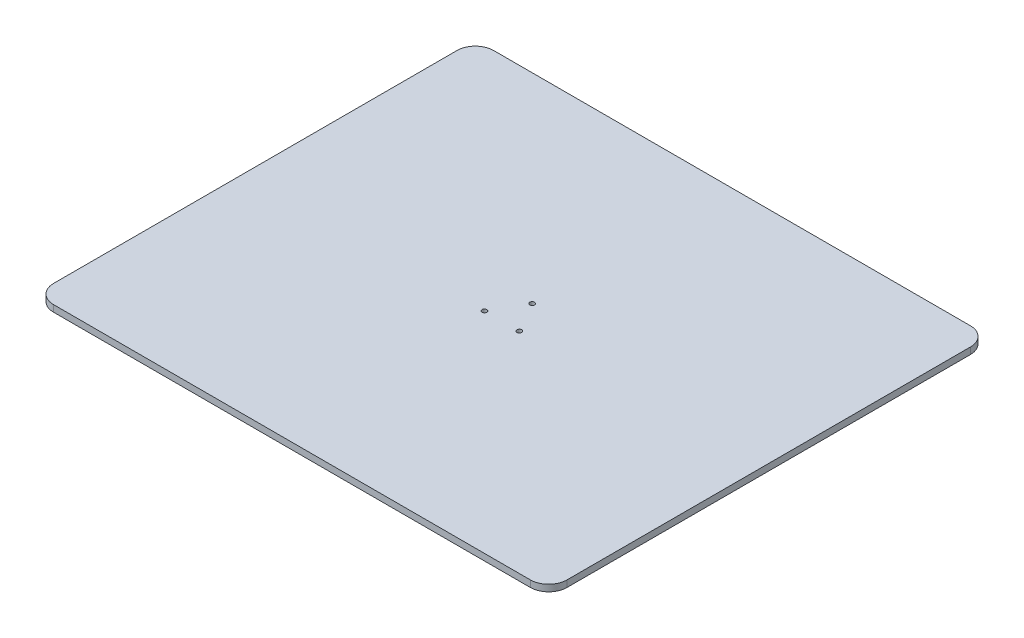
SolidWorks part; units mm, degrees
material "ABS"
ref_plane "Front Plane" through (0, 0, 0) normal (0, 0, 1) x (1, 0, 0)
ref_plane "Top Plane" through (0, 0, 0) normal (0, 1, 0) x (1, 0, 0)
ref_plane "Right Plane" through (0, 0, 0) normal (1, 0, 0) x (0, 0, -1)
sketch "Sketch1" plane through (0, 0, 0) normal (0, 1, 0) x (1, 0, 0)
  line L0 (55, 0) -> (-27.5, 47.6314) construction
  line L1 (-700, 600) -> (700, 600)
  line L2 (-700, 600) -> (-700, -600)
  line L3 (-700, -600) -> (700, -600)
  line L4 (700, 600) -> (700, -600)
  line L5 (0, -600) -> (0, 600) construction
  line L6 (-700, 0) -> (700, 0) construction
  line L7 (-27.5, 47.6314) -> (-27.5, -47.6314) construction
  line L8 (-27.5, -47.6314) -> (55, 0) construction
  line L9 (0, 0) -> (0, 55) construction
  line L10 (0, 55) -> (-47.6314, -27.5) construction
  line L11 (-47.6314, -27.5) -> (47.6314, -27.5) construction
  line L12 (47.6314, -27.5) -> (0, 55) construction
  circle A0 centre (0, 0) radius 75 construction
  circle A1 centre (0, 0) radius 55 construction
  circle A2 centre (0, 0) radius 27.5 construction
  circle A3 centre (0, 0) radius 27.5 construction
  circle A4 centre (0, 55) radius 6.5
  circle A5 centre (-47.6314, -27.5) radius 6.5
  circle A6 centre (47.6314, -27.5) radius 6.5
  point P0 (0, 0)
  dimension "D3" = 110
  dimension "D4" = 150
  dimension "D1" = 1400
  dimension "D2" = 1200
extrude "Boss-Extrude1" add sketch "Sketch1" along normal blind 18
sketch "Sketch2" plane through (0, 0, 0) normal (0, -1, 0) x (1, 0, 0)
  circle A0 centre (0, 0) radius 5
extrude "Cut-Extrude1" cut sketch "Sketch2" against normal blind 1
fillet "Fillet1" radius 50 4 edges at (700, 9, -600) (700, 9, 600) (-700, 9, 600) (-700, 9, -600)
sketch "Sketch3" plane through (0, 18, 0) normal (0, 1, 0) x (1, 0, 0)
  line L0 (-108.937, -219.6886) -> (-234.7326, -210.062)
  line L1 (-234.7326, -210.062) -> (-358.2136, -219.2576)
  line L2 (-24.6354, -235.7994) -> (-24.8453, -235.7994)
  line L3 (-40.5789, -291.8555) -> (-48.0791, -291.8555)
  line L4 (-63.7066, -235.7994) -> (-63.9144, -235.7994)
  line L5 (-68.808, -291.8555) -> (-79.9628, -291.8555)
  line L6 (-79.9628, -291.8555) -> (-71.9409, -220.1722)
  line L7 (-71.9409, -220.1722) -> (-58.6049, -220.1722)
  line L8 (-58.6049, -220.1722) -> (-45.7821, -266.1213)
  line L9 (-43.9096, -274.1443) -> (-43.7005, -274.1443)
  line L10 (-41.8247, -266.1213) -> (-28.5982, -220.1722)
  line L11 (-28.5982, -220.1722) -> (-15.2571, -220.1722)
  line L12 (-15.2571, -220.1722) -> (-7.2304, -291.8555)
  line L13 (-7.2304, -291.8555) -> (-19.7405, -291.8555)
  line L14 (4.7523, -235.6977) -> (17.4635, -235.6977)
  line L15 (17.4635, -235.6977) -> (17.4635, -291.8555)
  line L16 (17.4635, -291.8555) -> (4.7523, -291.8555)
  line L17 (4.7523, -291.8555) -> (4.7523, -235.6977)
  line L18 (62.3691, -283.5184) -> (62.3691, -243.0942)
  line L19 (62.3691, -236.2174) -> (62.3691, -210.0652)
  line L20 (62.3691, -210.0652) -> (75.0815, -210.0652)
  line L21 (75.0815, -210.0652) -> (75.0815, -288.8365)
  line L22 (119.5758, -283.5184) -> (119.5758, -243.0942)
  line L23 (119.5758, -236.2174) -> (119.5758, -210.0652)
  line L24 (119.5758, -210.0652) -> (132.2904, -210.0652)
  line L25 (132.2904, -210.0652) -> (132.2904, -288.8365)
  line L26 (146.9693, -210.0652) -> (159.6729, -210.0652)
  line L27 (159.6729, -210.0652) -> (159.6729, -291.8555)
  line L28 (159.6729, -291.8555) -> (146.9693, -291.8555)
  line L29 (146.9693, -291.8555) -> (146.9693, -210.0652)
  line L30 (183.0194, -261.9537) -> (206.2499, -258.4109)
  line L31 (213.2263, -280.9174) -> (216.2497, -288.9393)
  line L32 (218.1244, -263.4141) -> (183.7434, -268.415)
  line L33 (225.9145, -288.7294) -> (229.2617, -280.6033)
  line L34 (259.7856, -238.6117) -> (256.664, -246.0124)
  line L35 (281.883, -261.9537) -> (305.1112, -258.4109)
  line L36 (312.0987, -280.9174) -> (315.122, -288.9393)
  line L37 (316.988, -263.4141) -> (282.618, -268.415)
  line L38 (356.0547, -291.8555) -> (345.5278, -271.4349)
  line L39 (345.5278, -271.4349) -> (345.3244, -271.4349)
  line L40 (345.3244, -271.4349) -> (334.5832, -291.8555)
  line L41 (334.5832, -291.8555) -> (321.6674, -291.8555)
  line L42 (321.6674, -291.8555) -> (339.0722, -262.7895)
  line L43 (339.0722, -262.7895) -> (323.4394, -235.6977)
  line L44 (323.4394, -235.6977) -> (336.7839, -235.6977)
  line L45 (336.7839, -235.6977) -> (346.2608, -254.0335)
  line L46 (346.2608, -254.0335) -> (346.4664, -254.0335)
  line L47 (346.4664, -254.0335) -> (356.3632, -235.6977)
  line L48 (356.3632, -235.6977) -> (368.3383, -235.6977)
  line L49 (368.3383, -235.6977) -> (352.408, -261.9548)
  line L50 (352.408, -261.9548) -> (370.0119, -291.8555)
  line L51 (370.0119, -291.8555) -> (356.0547, -291.8555)
  line L52 (-77.3618, -371.7369) -> (-77.3618, -320.8951)
  line L53 (-77.3618, -320.8951) -> (-64.1232, -320.8951)
  line L54 (-64.1232, -320.8951) -> (-64.1232, -371.6363)
  line L55 (-42.3444, -371.6363) -> (-42.3444, -320.8951)
  line L56 (-42.3444, -320.8951) -> (-30.0518, -320.8951)
  line L57 (-30.0518, -320.8951) -> (-30.0518, -371.7369)
  line L58 (15.6893, -392.5764) -> (15.6893, -352.779)
  line L59 (-3.1681, -344.9679) -> (-3.1681, -392.5764)
  line L60 (-3.1681, -392.5764) -> (-15.8805, -392.5764)
  line L61 (-15.8805, -392.5764) -> (-15.8805, -339.4419)
  line L62 (28.4039, -352.5689) -> (28.4039, -392.5764)
  line L63 (28.4039, -392.5764) -> (15.6893, -392.5764)
  line L64 (42.3654, -336.4166) -> (55.0734, -336.4166)
  line L65 (55.0734, -336.4166) -> (55.0734, -392.572)
  line L66 (55.0734, -392.572) -> (42.3654, -392.572)
  line L67 (42.3654, -392.572) -> (42.3654, -336.4166)
  line L68 (94.8796, -392.5764) -> (82.7907, -392.5764)
  line L69 (82.7907, -392.5764) -> (64.454, -336.4197)
  line L70 (64.454, -336.4197) -> (77.9997, -336.4197)
  line L71 (77.9997, -336.4197) -> (87.8921, -372.6798)
  line L72 (89.253, -380.387) -> (89.4587, -380.387)
  line L73 (90.9199, -372.6798) -> (101.0203, -336.4197)
  line L74 (101.0203, -336.4197) -> (112.9013, -336.4197)
  line L75 (112.9013, -336.4197) -> (94.8796, -392.5764)
  line L76 (129.6629, -362.678) -> (152.8956, -359.1361)
  line L77 (159.8743, -381.6448) -> (162.9019, -389.6625)
  line L78 (164.7701, -364.1372) -> (130.3914, -369.1336)
  line L79 (189.0508, -345.1704) -> (189.0508, -392.5764)
  line L80 (189.0508, -392.5764) -> (176.3362, -392.5764)
  line L81 (176.3362, -392.5764) -> (176.3362, -339.441)
  line L82 (203.4345, -335.4791) -> (200.9273, -344.7569)
  line L83 (208.3216, -389.4568) -> (211.6511, -381.3276)
  line L84 (242.1817, -339.3391) -> (239.0643, -346.7378)
  line L85 (255.4214, -336.4166) -> (268.1337, -336.4166)
  line L86 (268.1337, -336.4166) -> (268.1337, -392.572)
  line L87 (268.1337, -392.572) -> (255.4214, -392.572)
  line L88 (255.4214, -392.572) -> (255.4214, -336.4166)
  line L89 (285.3221, -377.9893) -> (285.3221, -344.5467)
  line L90 (285.3221, -344.5467) -> (279.0784, -344.5467)
  line L91 (279.0784, -344.5467) -> (279.0784, -336.4166)
  line L92 (279.0784, -336.4166) -> (285.3221, -336.4166)
  line L93 (285.3221, -336.4166) -> (285.3221, -324.0181)
  line L94 (285.3221, -324.0181) -> (298.0432, -320.4785)
  line L95 (298.0432, -320.4785) -> (298.0432, -336.4166)
  line L96 (298.0432, -336.4166) -> (307.2026, -336.4166)
  line L97 (307.2026, -336.4166) -> (307.2026, -344.5467)
  line L98 (307.2026, -344.5467) -> (298.0432, -344.5467)
  line L99 (298.0432, -344.5467) -> (298.0432, -377.3679)
  line L100 (307.2026, -384.143) -> (307.2026, -392.0536)
  line L101 (336.0729, -414.9778) -> (322.63, -414.9778)
  line L102 (322.63, -414.9778) -> (331.796, -392.572)
  line L103 (331.796, -392.572) -> (313.2472, -336.4186)
  line L104 (313.2472, -336.4186) -> (326.8018, -336.4186)
  line L105 (326.8018, -336.4186) -> (336.4864, -372.7826)
  line L106 (337.6304, -380.809) -> (337.8406, -380.809)
  line L107 (339.3916, -372.7826) -> (349.8222, -336.4186)
  line L108 (349.8222, -336.4186) -> (361.7012, -336.4186)
  line L109 (361.7012, -336.4186) -> (336.0729, -414.9778)
  line L110 (-76.4178, -496.7756) -> (-76.4178, -425.0979)
  line L111 (-76.4178, -425.0979) -> (-66.8338, -425.0979)
  line L112 (-66.8338, -425.0979) -> (-66.8338, -490.3155)
  line L113 (-66.8338, -490.3155) -> (-45.2626, -490.3155)
  line L114 (-45.2626, -490.3155) -> (-45.2626, -496.7756)
  line L115 (-45.2626, -496.7756) -> (-76.4178, -496.7756)
  line L116 (50.2847, -496.7756) -> (50.2847, -456.4531)
  line L117 (27.8811, -447.497) -> (27.8811, -496.7756)
  line L118 (27.8811, -496.7756) -> (18.7149, -496.7756)
  line L119 (18.7149, -496.7756) -> (18.7149, -443.5286)
  line L120 (59.4574, -456.2497) -> (59.4574, -496.7756)
  line L121 (59.4574, -496.7756) -> (50.2847, -496.7756)
  line L122 (105.2927, -490.2149) -> (105.2927, -446.4491)
  line L123 (105.2927, -441.3431) -> (105.2927, -414.9821)
  line L124 (105.2927, -414.9821) -> (114.3605, -414.9821)
  line L125 (114.3605, -414.9821) -> (114.3605, -493.8661)
  line L126 (215.0113, -496.7756) -> (215.0113, -456.4531)
  line L127 (192.6099, -447.497) -> (192.6099, -496.7756)
  line L128 (192.6099, -496.7756) -> (183.4482, -496.7756)
  line L129 (183.4482, -496.7756) -> (183.4482, -443.5286)
  line L130 (224.1862, -456.2497) -> (224.1862, -496.7756)
  line L131 (224.1862, -496.7756) -> (215.0113, -496.7756)
  line L132 (-287.6033, -317.3665) -> (-287.8495, -317.476)
  line L133 (-283.8428, -360.4576) -> (-283.5695, -360.357)
  line L134 (-192.9487, -354.5454) -> (-186.1037, -360.9652)
  line L135 (-186.1037, -360.9652) -> (-145.5361, -360.9652)
  line L136 (-145.5361, -360.9652) -> (-145.5361, -360.2519)
  line L137 (-277.5347, -373.0626) -> (-277.7809, -373.1612)
  line L138 (-275.9499, -402.3069) -> (-275.9958, -402.3069)
  line L139 (-274.3748, -408.5417) -> (-274.1517, -408.4521)
  line L140 (-201.5593, -403.3986) -> (-195.3584, -408.8304)
  line L141 (-195.3584, -408.8304) -> (-162.7178, -408.8304)
  line L142 (-162.7178, -408.8304) -> (-162.7178, -408.1152)
  line L143 (-231.3232, -424.039) -> (-231.8711, -424.0345)
  line L144 (-264.1125, -430.4095) -> (-265.003, -430.72)
  line L145 (-266.9904, -420.6875) -> (-267.1687, -420.7664)
  line L146 (-264.2767, -450.8113) -> (-264.037, -450.715)
  line L147 (-210.0286, -445.6659) -> (-205.3461, -449.4549)
  line L148 (-205.3461, -449.4549) -> (-180.6346, -449.4549)
  line L149 (-180.6346, -449.4549) -> (-180.6346, -448.7417)
  line L150 (-204.3125, -247.2035) -> (-207.3172, -248.2963)
  line L151 (-207.3172, -248.2963) -> (-205.3165, -253.8025)
  line L152 (-230.9809, -246.1775) -> (-226.8288, -242.0398)
  line L153 (-226.8288, -242.0398) -> (-229.0962, -239.7799)
  line L154 (-239.3222, -239.7777) -> (-241.5767, -242.0342)
  line L155 (-241.5767, -242.0342) -> (-237.4244, -246.1896)
  line L156 (-262.6327, -253.7983) -> (-260.6331, -248.2963)
  line L157 (-260.6331, -248.2963) -> (-263.6412, -247.2035)
  line L158 (-272.9102, -251.5263) -> (-273.9951, -254.5279)
  line L159 (-273.9951, -254.5279) -> (-268.4474, -256.5492)
  line L160 (-199.528, -256.5579) -> (-193.9518, -254.5279)
  line L161 (-193.9518, -254.5279) -> (-195.0412, -251.5263)
  spline S0 degree 2 poles (-358.2136, -219.2576) (-359.0843, -246.2586) (-359.0843, -279.7218) knots 2 2 2 3 3 3
  spline S1 degree 2 poles (-359.0843, -279.7218) (-359.0843, -451.1395) (-233.9723, -496.7953) knots 3 3 3 4 4 4
  spline S2 degree 2 poles (-233.9723, -496.7953) (-108.0609, -451.5748) (-108.0609, -280.1549) knots 4 4 4 5 5 5
  spline S3 degree 2 poles (-108.0609, -280.1549) (-108.0609, -246.6939) (-108.937, -219.6886) knots 5 5 5 6 6 6
  spline S4 degree 2 poles (-19.7405, -291.8555) (-19.8402, -290.0867) (-24.3225, -244.4495) knots 0 0 0 1 1 1
  spline S5 degree 2 poles (-24.3225, -244.4495) (-24.7337, -239.9659) (-24.6354, -235.7994) knots 1 1 1 2 2 2
  spline S6 degree 2 poles (-24.8453, -235.7994) (-25.5716, -239.863) (-26.9226, -244.4495) knots 3 3 3 4 4 4
  spline S7 degree 2 poles (-26.9226, -244.4495) (-39.742, -289.4622) (-40.5789, -291.8555) knots 4 4 4 5 5 5
  spline S8 degree 2 poles (-48.0791, -291.8555) (-48.8043, -289.7729) (-61.6185, -244.3433) knots 6 6 6 7 7 7
  spline S9 degree 2 poles (-61.6185, -244.3433) (-62.8676, -239.863) (-63.7066, -235.7994) knots 7 7 7 8 8 8
  spline S10 degree 2 poles (-63.9144, -235.7994) (-63.8136, -239.863) (-64.226, -244.3433) knots 9 9 9 10 10 10
  spline S11 degree 2 poles (-64.226, -244.3433) (-68.7086, -289.7729) (-68.808, -291.8555) knots 10 10 10 11 11 11
  spline S12 degree 2 poles (-45.7821, -266.1213) (-44.5395, -270.7021) (-43.9096, -274.1443) knots 15 15 15 16 16 16
  spline S13 degree 2 poles (-43.7005, -274.1443) (-43.1788, -270.7021) (-41.8247, -266.1213) knots 17 17 17 18 18 18
  spline S14 degree 3 poles (11.1107, -213.4003) (15.0724, -213.4003) (18.0892, -216.2103) (18.0892, -219.7553) (18.0892, -223.1922) (15.0724, -226.0064) (11.1107, -226.0064) knots 2 2 2 2 3 3 3 4 4 4 4
  spline S15 degree 3 poles (11.1107, -226.0064) (7.2539, -226.0064) (4.1298, -223.1922) (4.1298, -219.7553) (4.1298, -216.2103) (7.2539, -213.4003) (11.1107, -213.4003) knots 0 0 0 0 1 1 1 2 2 2 2
  spline S16 degree 3 poles (62.3691, -243.0942) (60.5992, -242.5725) (58.7267, -242.3657) (56.7446, -242.3657) knots 0 0 0 0 1 1 1 1
  spline S17 degree 3 poles (56.7446, -242.3657) (45.6949, -242.3657) (41.9453, -251.8458) (41.9453, -263.7268) knots 1 1 1 1 2 2 2 2
  spline S18 degree 3 poles (41.9453, -263.7268) (41.9453, -276.4371) (46.0166, -284.772) (55.8127, -284.772) knots 2 2 2 2 3 3 3 3
  spline S19 degree 3 poles (55.8127, -284.772) (58.823, -284.772) (60.9144, -284.4602) (62.3691, -283.5184) knots 3 3 3 3 4 4 4 4
  spline S20 degree 3 poles (55.4935, -292.899) (38.9243, -292.899) (29.3423, -282.2713) (29.3423, -264.4542) knots 0 0 0 0 1 1 1 1
  spline S21 degree 3 poles (29.3423, -264.4542) (29.3423, -246.1175) (39.3443, -235.1749) (53.9357, -235.1749) knots 1 1 1 1 2 2 2 2
  spline S22 degree 3 poles (53.9357, -235.1749) (57.064, -235.1749) (59.8729, -235.4898) (62.3691, -236.2174) knots 2 2 2 2 3 3 3 3
  spline S23 degree 3 poles (75.0815, -288.8365) (70.6012, -291.3381) (64.2439, -292.899) (55.4935, -292.899) knots 6 6 6 6 7 7 7 7
  spline S24 degree 3 poles (119.5758, -243.0942) (117.8081, -242.5725) (115.9158, -242.3657) (113.947, -242.3657) knots 0 0 0 0 1 1 1 1
  spline S25 degree 3 poles (113.947, -242.3657) (102.9038, -242.3657) (99.1542, -251.8458) (99.1542, -263.7268) knots 1 1 1 1 2 2 2 2
  spline S26 degree 3 poles (99.1542, -263.7268) (99.1542, -276.4371) (103.208, -284.772) (113.0063, -284.772) knots 2 2 2 2 3 3 3 3
  spline S27 degree 3 poles (113.0063, -284.772) (116.0339, -284.772) (118.1078, -284.4602) (119.5758, -283.5184) knots 3 3 3 3 4 4 4 4
  spline S28 degree 3 poles (112.7044, -292.899) (96.1309, -292.899) (86.5447, -282.2713) (86.5447, -264.4542) knots 0 0 0 0 1 1 1 1
  spline S29 degree 3 poles (86.5447, -264.4542) (86.5447, -246.1175) (96.5465, -235.1749) (111.1316, -235.1749) knots 1 1 1 1 2 2 2 2
  spline S30 degree 3 poles (111.1316, -235.1749) (114.2577, -235.1749) (117.0753, -235.4898) (119.5758, -236.2174) knots 2 2 2 2 3 3 3 3
  spline S31 degree 3 poles (132.2904, -288.8365) (127.8078, -291.3381) (121.4528, -292.899) (112.7044, -292.899) knots 6 6 6 6 7 7 7 7
  spline S32 degree 3 poles (195.2002, -242.4663) (187.8104, -242.4663) (182.7045, -248.5129) (183.0194, -261.9537) knots 0 0 0 0 1 1 1 1
  spline S33 degree 3 poles (206.2499, -258.4109) (206.2499, -247.0548) (202.1831, -242.4663) (195.2002, -242.4663) knots 2 2 2 2 3 3 3 3
  spline S34 degree 3 poles (183.7434, -268.415) (184.7782, -278.8336) (189.7835, -284.039) (199.0548, -284.039) knots 0 0 0 0 1 1 1 1
  spline S35 degree 3 poles (199.0548, -284.039) (205.5172, -284.039) (210.2096, -282.4803) (213.2263, -280.9174) knots 1 1 1 1 2 2 2 2
  spline S36 degree 3 poles (216.2497, -288.9393) (212.29, -291.1271) (206.2499, -292.899) (197.7029, -292.899) knots 3 3 3 3 4 4 4 4
  spline S37 degree 3 poles (197.7029, -292.899) (181.7636, -292.899) (171.6525, -282.5843) (171.6525, -263.6208) knots 4 4 4 4 5 5 5 5
  spline S38 degree 3 poles (171.6525, -263.6208) (171.6525, -245.2828) (180.9303, -234.6531) (195.6312, -234.6531) knots 5 5 5 5 6 6 6 6
  spline S39 degree 3 poles (195.6312, -234.6531) (210.518, -234.6531) (218.6428, -244.5532) (218.1244, -263.4141) knots 6 6 6 6 7 7 7 7
  spline S40 degree 3 poles (241.4467, -292.7951) (234.8818, -292.7951) (229.2617, -291.0242) (225.9145, -288.7294) knots 0 0 0 0 1 1 1 1
  spline S41 degree 3 poles (229.2617, -280.6033) (231.3444, -282.2713) (235.1968, -283.8356) (239.7821, -283.8356) knots 2 2 2 2 3 3 3 3
  spline S42 degree 3 poles (239.7821, -283.8356) (244.9864, -283.8356) (248.4209, -280.4983) (248.4209, -275.9131) knots 3 3 3 3 4 4 4 4
  spline S43 degree 3 poles (248.4209, -275.9131) (248.4209, -271.121) (245.9227, -268.8296) (240.1911, -266.6441) knots 4 4 4 4 5 5 5 5
  spline S44 degree 3 poles (240.1911, -266.6441) (229.5679, -262.5794) (227.3825, -256.7472) (227.3825, -250.9105) knots 5 5 5 5 6 6 6 6
  spline S45 degree 3 poles (227.3825, -250.9105) (227.3825, -241.9479) (234.4595, -234.6531) (245.1963, -234.6531) knots 6 6 6 6 7 7 7 7
  spline S46 degree 3 poles (245.1963, -234.6531) (251.4442, -234.6531) (256.1259, -236.2174) (259.7856, -238.6117) knots 7 7 7 7 8 8 8 8
  spline S47 degree 3 poles (256.664, -246.0124) (254.9969, -244.6551) (251.6586, -242.8863) (247.699, -242.8863) knots 9 9 9 9 10 10 10 10
  spline S48 degree 3 poles (247.699, -242.8863) (242.4837, -242.8863) (239.6748, -246.3263) (239.6748, -250.2817) knots 10 10 10 10 11 11 11 11
  spline S49 degree 3 poles (239.6748, -250.2817) (239.6748, -254.8668) (243.1138, -257.1574) (248.0074, -259.1394) knots 11 11 11 11 12 12 12 12
  spline S50 degree 3 poles (248.0074, -259.1394) (258.9523, -263.5169) (261.4505, -269.1446) (261.4505, -275.7041) knots 12 12 12 12 13 13 13 13
  spline S51 degree 3 poles (261.4505, -275.7041) (261.4505, -284.8757) (253.7368, -292.7951) (241.4467, -292.7951) knots 13 13 13 13 14 14 14 14
  spline S52 degree 3 poles (294.0725, -242.4663) (286.6673, -242.4663) (281.5658, -248.5129) (281.883, -261.9537) knots 0 0 0 0 1 1 1 1
  spline S53 degree 3 poles (305.1112, -258.4109) (305.1112, -247.0548) (301.0532, -242.4663) (294.0725, -242.4663) knots 2 2 2 2 3 3 3 3
  spline S54 degree 3 poles (282.618, -268.415) (283.6572, -278.8336) (288.6559, -284.039) (297.9206, -284.039) knots 0 0 0 0 1 1 1 1
  spline S55 degree 3 poles (297.9206, -284.039) (304.3828, -284.039) (309.0709, -282.4803) (312.0987, -280.9174) knots 1 1 1 1 2 2 2 2
  spline S56 degree 3 poles (315.122, -288.9393) (311.1623, -291.1271) (305.1112, -292.899) (296.5707, -292.899) knots 3 3 3 3 4 4 4 4
  spline S57 degree 3 poles (296.5707, -292.899) (280.6317, -292.899) (270.5271, -282.5843) (270.5271, -263.6208) knots 4 4 4 4 5 5 5 5
  spline S58 degree 3 poles (270.5271, -263.6208) (270.5271, -245.2828) (279.7916, -234.6531) (294.4816, -234.6531) knots 5 5 5 5 6 6 6 6
  spline S59 degree 3 poles (294.4816, -234.6531) (309.3881, -234.6531) (317.5151, -244.5532) (316.988, -263.4141) knots 6 6 6 6 7 7 7 7
  spline S60 degree 3 poles (-53.7057, -393.725) (-67.769, -393.725) (-77.3618, -384.7599) (-77.3618, -371.7369) knots 0 0 0 0 1 1 1 1
  spline S61 degree 3 poles (-64.1232, -371.6363) (-64.1232, -379.3455) (-59.1158, -383.5108) (-53.1797, -383.5108) knots 4 4 4 4 5 5 5 5
  spline S62 degree 3 poles (-53.1797, -383.5108) (-47.1407, -383.5108) (-42.3444, -379.3455) (-42.3444, -371.6363) knots 5 5 5 5 6 6 6 6
  spline S63 degree 3 poles (-30.0518, -371.7369) (-30.0518, -384.7599) (-39.6372, -393.725) (-53.7057, -393.725) knots 9 9 9 9 10 10 10 10
  spline S64 degree 3 poles (15.6893, -352.779) (15.6893, -348.1948) (13.6024, -343.4027) (5.5868, -343.4027) knots 1 1 1 1 2 2 2 2
  spline S65 degree 3 poles (5.5868, -343.4027) (1.4161, -343.4027) (-0.7705, -344.023) (-3.1681, -344.9679) knots 2 2 2 2 3 3 3 3
  spline S66 degree 3 poles (-15.8805, -339.4419) (-10.5689, -336.9437) (-3.3792, -335.3839) (6.1065, -335.3839) knots 6 6 6 6 7 7 7 7
  spline S67 degree 3 poles (6.1065, -335.3839) (22.8802, -335.3839) (28.4039, -343.5044) (28.4039, -352.5689) knots 7 7 7 7 8 8 8 8
  spline S68 degree 3 poles (48.7227, -314.1212) (52.6888, -314.1212) (55.6989, -316.9377) (55.6989, -320.4785) (55.6989, -323.9187) (52.6888, -326.7307) (48.7227, -326.7307) knots 2 2 2 2 3 3 3 4 4 4 4
  spline S69 degree 3 poles (48.7227, -326.7307) (44.8723, -326.7307) (41.7374, -323.9187) (41.7374, -320.4785) (41.7374, -316.9377) (44.8723, -314.1212) (48.7227, -314.1212) knots 0 0 0 0 1 1 1 2 2 2 2
  spline S70 degree 2 poles (87.8921, -372.6798) (89.0451, -376.7445) (89.253, -380.387) knots 4 4 4 5 5 5
  spline S71 degree 2 poles (89.4587, -380.387) (89.7779, -376.8473) (90.9199, -372.6798) knots 6 6 6 7 7 7
  spline S72 degree 3 poles (141.8524, -343.1928) (134.4494, -343.1928) (129.3392, -349.236) (129.6629, -362.678) knots 0 0 0 0 1 1 1 1
  spline S73 degree 3 poles (152.8956, -359.1361) (152.8956, -347.7802) (148.8354, -343.1928) (141.8524, -343.1928) knots 2 2 2 2 3 3 3 3
  spline S74 degree 3 poles (130.3914, -369.1336) (131.4306, -379.5579) (136.4292, -384.7599) (145.6983, -384.7599) knots 0 0 0 0 1 1 1 1
  spline S75 degree 3 poles (145.6983, -384.7599) (152.1606, -384.7599) (156.8508, -383.2046) (159.8743, -381.6448) knots 1 1 1 1 2 2 2 2
  spline S76 degree 3 poles (162.9019, -389.6625) (158.9335, -391.8502) (152.8956, -393.6199) (144.3421, -393.6199) knots 3 3 3 3 4 4 4 4
  spline S77 degree 3 poles (144.3421, -393.6199) (128.4073, -393.6199) (118.3005, -383.3052) (118.3005, -364.3429) knots 4 4 4 4 5 5 5 5
  spline S78 degree 3 poles (118.3005, -364.3429) (118.3005, -346.0028) (127.5672, -335.3817) (142.2594, -335.3817) knots 5 5 5 5 6 6 6 6
  spline S79 degree 3 poles (142.2594, -335.3817) (157.1615, -335.3817) (165.2952, -345.2786) (164.7701, -364.1372) knots 6 6 6 6 7 7 7 7
  spline S80 degree 3 poles (200.9273, -344.7569) (196.6572, -343.301) (191.9712, -343.5044) (189.0508, -345.1704) knots 0 0 0 0 1 1 1 1
  spline S81 degree 3 poles (176.3362, -339.441) (182.1662, -336.6276) (189.2564, -335.0624) (203.4345, -335.4791) knots 4 4 4 4 5 5 5 5
  spline S82 degree 3 poles (223.8451, -393.5171) (217.2844, -393.5171) (211.6511, -391.7364) (208.3216, -389.4568) knots 0 0 0 0 1 1 1 1
  spline S83 degree 3 poles (211.6511, -381.3276) (213.7382, -382.999) (217.6016, -384.5565) (222.1824, -384.5565) knots 2 2 2 2 3 3 3 3
  spline S84 degree 3 poles (222.1824, -384.5565) (227.389, -384.5565) (230.8323, -381.2248) (230.8323, -376.6372) knots 3 3 3 3 4 4 4 4
  spline S85 degree 3 poles (230.8323, -376.6372) (230.8323, -371.8464) (228.3276, -369.5536) (222.6002, -367.3617) knots 4 4 4 4 5 5 5 5
  spline S86 degree 3 poles (222.6002, -367.3617) (211.9705, -363.3014) (209.783, -357.4726) (209.783, -351.6337) knots 5 5 5 5 6 6 6 6
  spline S87 degree 3 poles (209.783, -351.6337) (209.783, -342.6666) (216.8708, -335.3839) (227.6013, -335.3839) knots 6 6 6 6 7 7 7 7
  spline S88 degree 3 poles (227.6013, -335.3839) (233.8535, -335.3839) (238.5372, -336.9415) (242.1817, -339.3391) knots 7 7 7 7 8 8 8 8
  spline S89 degree 3 poles (239.0643, -346.7378) (237.4062, -345.3792) (234.0634, -343.6117) (230.0995, -343.6117) knots 9 9 9 9 10 10 10 10
  spline S90 degree 3 poles (230.0995, -343.6117) (224.8885, -343.6117) (222.0861, -347.0483) (222.0861, -351.0057) knots 10 10 10 10 11 11 11 11
  spline S91 degree 3 poles (222.0861, -351.0057) (222.0861, -355.5922) (225.5164, -357.8827) (230.4167, -359.8581) knots 11 11 11 11 12 12 12 12
  spline S92 degree 3 poles (230.4167, -359.8581) (241.3527, -364.242) (243.8531, -369.8731) (243.8531, -376.4315) knots 12 12 12 12 13 13 13 13
  spline S93 degree 3 poles (243.8531, -376.4315) (243.8531, -385.5977) (236.1418, -393.5171) (223.8451, -393.5171) knots 13 13 13 13 14 14 14 14
  spline S94 degree 3 poles (261.7829, -314.1212) (265.7361, -314.1212) (268.7616, -316.9377) (268.7616, -320.4785) (268.7616, -323.9187) (265.7361, -326.7307) (261.7829, -326.7307) knots 2 2 2 2 3 3 3 4 4 4 4
  spline S95 degree 3 poles (261.7829, -326.7307) (257.9241, -326.7307) (254.7957, -323.9187) (254.7957, -320.4785) (254.7957, -316.9377) (257.9241, -314.1212) (261.7829, -314.1212) knots 0 0 0 0 1 1 1 2 2 2 2
  spline S96 degree 3 poles (300.7492, -393.2021) (289.6973, -393.2021) (285.3221, -385.8079) (285.3221, -377.9893) knots 0 0 0 0 1 1 1 1
  spline S97 degree 3 poles (298.0432, -377.3679) (298.0432, -381.7476) (299.8086, -384.6593) (304.1838, -384.6593) knots 12 12 12 12 13 13 13 13
  spline S98 degree 3 poles (304.1838, -384.6593) (305.3301, -384.6593) (306.1679, -384.4515) (307.2026, -384.143) knots 13 13 13 13 14 14 14 14
  spline S99 degree 3 poles (307.2026, -392.0536) (306.0564, -392.5764) (303.7638, -393.2021) (300.7492, -393.2021) knots 15 15 15 15 16 16 16 16
  spline S100 degree 2 poles (336.4864, -372.7826) (337.6304, -377.1623) (337.6304, -380.809) knots 5 5 5 6 6 6
  spline S101 degree 2 poles (337.8406, -380.809) (338.1578, -377.1623) (339.3916, -372.7826) knots 7 7 7 8 8 8
  spline S102 degree 3 poles (-15.7765, -491.4663) (-5.0429, -491.4663) (-3.0676, -480.003) (-3.0676, -468.7477) (-3.0676, -457.4966) (-5.0429, -445.4079) (-15.7765, -445.4079) knots 2 2 2 2 3 3 3 4 4 4 4
  spline S103 degree 3 poles (-15.7765, -445.4079) (-26.5079, -445.4079) (-28.596, -457.3917) (-28.596, -468.7477) (-28.596, -480.1126) (-26.3056, -491.4663) (-15.7765, -491.4663) knots 0 0 0 0 1 1 1 2 2 2 2
  spline S104 degree 3 poles (-15.8805, -439.5777) (-0.4632, -439.5777) (6.1065, -451.9751) (6.1065, -468.7477) (6.1065, -485.214) (-0.566, -497.8258) (-15.7765, -497.8258) knots 2 2 2 2 3 3 3 4 4 4 4
  spline S105 degree 3 poles (-15.7765, -497.8258) (-31.0986, -497.8258) (-37.7633, -485.214) (-37.7633, -468.7477) (-37.7633, -451.9751) (-30.9871, -439.5777) (-15.8805, -439.5777) knots 0 0 0 0 1 1 1 2 2 2 2
  spline S106 degree 3 poles (50.2847, -456.4531) (50.2847, -451.2443) (48.0992, -445.515) (38.5085, -445.515) knots 1 1 1 1 2 2 2 2
  spline S107 degree 3 poles (38.5085, -445.515) (33.3065, -445.515) (30.8015, -446.2457) (27.8811, -447.497) knots 2 2 2 2 3 3 3 3
  spline S108 degree 3 poles (18.7149, -443.5286) (23.718, -441.1375) (30.2787, -439.5777) (39.2435, -439.5777) knots 6 6 6 6 7 7 7 7
  spline S109 degree 3 poles (39.2435, -439.5777) (54.8589, -439.5777) (59.4574, -448.2255) (59.4574, -456.2497) knots 7 7 7 7 8 8 8 8
  spline S110 degree 3 poles (105.2927, -446.4491) (103.0044, -445.8279) (100.7118, -445.4079) (98.3097, -445.4079) knots 0 0 0 0 1 1 1 1
  spline S111 degree 3 poles (98.3097, -445.4079) (85.2934, -445.4079) (81.1258, -456.6565) (81.1258, -468.8505) knots 1 1 1 1 2 2 2 2
  spline S112 degree 3 poles (81.1258, -468.8505) (81.1258, -482.0857) (85.7069, -491.7747) (97.1679, -491.7747) knots 2 2 2 2 3 3 3 3
  spline S113 degree 3 poles (97.1679, -491.7747) (100.9217, -491.7747) (103.5207, -491.3612) (105.2927, -490.2149) knots 3 3 3 3 4 4 4 4
  spline S114 degree 3 poles (96.7479, -497.8258) (80.7125, -497.8258) (72.0582, -486.5682) (72.0582, -469.5812) knots 0 0 0 0 1 1 1 1
  spline S115 degree 3 poles (72.0582, -469.5812) (72.0582, -450.9339) (81.9551, -440.0918) (96.4349, -440.0918) knots 1 1 1 1 2 2 2 2
  spline S116 degree 3 poles (96.4349, -440.0918) (99.5588, -440.0918) (102.2738, -440.5163) (105.2927, -441.3431) knots 2 2 2 2 3 3 3 3
  spline S117 degree 3 poles (114.3605, -493.8661) (110.6087, -496.1544) (104.5664, -497.8258) (96.7479, -497.8258) knots 6 6 6 6 7 7 7 7
  spline S118 degree 3 poles (148.9536, -491.4663) (159.6949, -491.4663) (161.6702, -480.003) (161.6702, -468.7477) (161.6702, -457.4966) (159.6949, -445.4079) (148.9536, -445.4079) knots 2 2 2 2 3 3 3 4 4 4 4
  spline S119 degree 3 poles (148.9536, -445.4079) (138.2296, -445.4079) (136.134, -457.3917) (136.134, -468.7477) (136.134, -480.1126) (138.4333, -491.4663) (148.9536, -491.4663) knots 0 0 0 0 1 1 1 2 2 2 2
  spline S120 degree 3 poles (148.8486, -439.5777) (164.267, -439.5777) (170.8387, -451.9751) (170.8387, -468.7477) (170.8387, -485.214) (164.1707, -497.8258) (148.9536, -497.8258) knots 2 2 2 2 3 3 3 4 4 4 4
  spline S121 degree 3 poles (148.9536, -497.8258) (133.6378, -497.8258) (126.9765, -485.214) (126.9765, -468.7477) (126.9765, -451.9751) (133.7494, -439.5777) (148.8486, -439.5777) knots 0 0 0 0 1 1 1 2 2 2 2
  spline S122 degree 3 poles (215.0113, -456.4531) (215.0113, -451.2443) (212.8281, -445.515) (203.2463, -445.515) knots 1 1 1 1 2 2 2 2
  spline S123 degree 3 poles (203.2463, -445.515) (198.031, -445.515) (195.5284, -446.2457) (192.6099, -447.497) knots 2 2 2 2 3 3 3 3
  spline S124 degree 3 poles (183.4482, -443.5286) (188.4491, -441.1375) (195.0033, -439.5777) (203.9681, -439.5777) knots 6 6 6 6 7 7 7 7
  spline S125 degree 3 poles (203.9681, -439.5777) (219.5966, -439.5777) (224.1862, -448.2255) (224.1862, -456.2497) knots 7 7 7 7 8 8 8 8
  spline S126 degree 3 poles (-229.5523, -319.5531) (-254.0144, -319.5531) (-276.1806, -327.4932) (-285.2594, -331.2363) knots 0 0 0 0 1 1 1 1
  spline S127 degree 3 poles (-285.2594, -331.2363) (-286.2547, -328.0893) (-285.9397, -326.0067) (-285.3885, -324.7159) knots 1 1 1 1 2 2 2 2
  spline S128 degree 3 poles (-285.3885, -324.7159) (-283.3013, -324.5398) (-281.653, -322.8544) (-281.653, -320.81) knots 2 2 2 2 3 3 3 3
  spline S129 degree 3 poles (-281.653, -320.81) (-281.653, -318.6496) (-283.4906, -316.8951) (-285.7516, -316.8951) knots 3 3 3 3 4 4 4 4
  spline S130 degree 3 poles (-285.7516, -316.8951) (-285.9516, -316.8951) (-286.1113, -316.9388) (-286.3159, -316.9935) knots 4 4 4 4 5 5 5 5
  spline S131 degree 3 poles (-286.3159, -316.9935) (-286.5435, -317.0188) (-286.7502, -317.0602) (-286.981, -317.1248) knots 5 5 5 5 6 6 6 6
  spline S132 degree 3 poles (-286.981, -317.1248) (-287.2063, -317.1884) (-287.4086, -317.2726) (-287.6033, -317.3665) knots 6 6 6 6 7 7 7 7
  spline S133 degree 3 poles (-287.8495, -317.476) (-287.8988, -317.511) (-288.0889, -317.6335) (-288.2979, -317.8062) knots 8 8 8 8 9 9 9 9
  spline S134 degree 3 poles (-288.2979, -317.8062) (-288.463, -317.9343) (-288.6098, -318.0513) (-288.7321, -318.1693) knots 9 9 9 9 10 10 10 10
  spline S135 degree 3 poles (-288.7321, -318.1693) (-290.0645, -319.377) (-294.1346, -323.8967) (-291.7621, -332.4175) knots 10 10 10 10 11 11 11 11
  spline S136 degree 3 poles (-291.7621, -332.4175) (-293.1534, -332.9908) (-294.1673, -334.243) (-294.6552, -335.9397) knots 11 11 11 11 12 12 12 12
  spline S137 degree 3 poles (-294.6552, -335.9397) (-295.9984, -335.2636) (-297.4117, -335.1379) (-298.6335, -335.6126) knots 12 12 12 12 13 13 13 13
  spline S138 degree 3 poles (-298.6335, -335.6126) (-300.0795, -336.1682) (-301.1393, -337.495) (-301.5923, -339.2549) knots 13 13 13 13 14 14 14 14
  spline S139 degree 3 poles (-301.5923, -339.2549) (-302.9431, -338.5167) (-304.3683, -338.3689) (-305.6044, -338.8339) knots 14 14 14 14 15 15 15 15
  spline S140 degree 3 poles (-305.6044, -338.8339) (-307.0799, -339.4059) (-308.1169, -340.7645) (-308.5127, -342.5671) knots 15 15 15 15 16 16 16 16
  spline S141 degree 3 poles (-308.5127, -342.5671) (-309.8582, -341.7663) (-311.3391, -341.586) (-312.5752, -342.0694) knots 16 16 16 16 17 17 17 17
  spline S142 degree 3 poles (-312.5752, -342.0694) (-314.0508, -342.6415) (-315.0714, -344.0591) (-315.4137, -345.9164) knots 17 17 17 17 18 18 18 18
  spline S143 degree 3 poles (-315.4137, -345.9164) (-316.747, -345.0346) (-318.2358, -344.7974) (-319.5472, -345.2929) knots 18 18 18 18 19 19 19 19
  spline S144 degree 3 poles (-319.5472, -345.2929) (-322.1319, -346.3023) (-323.1502, -349.9656) (-321.8048, -353.456) knots 19 19 19 19 20 20 20 20
  spline S145 degree 3 poles (-321.8048, -353.456) (-320.465, -356.9146) (-317.26, -358.9874) (-314.625, -357.9681) knots 20 20 20 20 21 21 21 21
  spline S146 degree 3 poles (-314.625, -357.9681) (-313.2786, -357.4385) (-312.3225, -356.1643) (-311.9518, -354.5006) knots 21 21 21 21 22 22 22 22
  spline S147 degree 3 poles (-311.9518, -354.5006) (-310.5123, -355.5212) (-308.8584, -355.8252) (-307.4518, -355.2815) knots 22 22 22 22 23 23 23 23
  spline S148 degree 3 poles (-307.4518, -355.2815) (-306.1185, -354.7598) (-305.1438, -353.5534) (-304.7161, -351.9486) knots 23 23 23 23 24 24 24 24
  spline S149 degree 3 poles (-304.7161, -351.9486) (-303.2778, -352.8839) (-301.6599, -353.1278) (-300.2852, -352.5951) knots 24 24 24 24 25 25 25 25
  spline S150 degree 3 poles (-300.2852, -352.5951) (-298.9561, -352.0844) (-297.9794, -350.9184) (-297.5067, -349.3346) knots 25 25 25 25 26 26 26 26
  spline S151 degree 3 poles (-297.5067, -349.3346) (-296.0443, -350.2237) (-294.4473, -350.4271) (-293.1064, -349.9087) knots 26 26 26 26 27 27 27 27
  spline S152 degree 3 poles (-293.1064, -349.9087) (-291.8004, -349.4034) (-290.8136, -348.2723) (-290.2986, -346.7367) knots 27 27 27 27 28 28 28 28
  spline S153 degree 3 poles (-290.2986, -346.7367) (-288.8318, -347.557) (-287.2686, -347.7387) (-285.9288, -347.2201) knots 28 28 28 28 29 29 29 29
  spline S154 degree 3 poles (-285.9288, -347.2201) (-285.6891, -347.126) (-285.4595, -347.008) (-285.231, -346.8624) knots 29 29 29 29 30 30 30 30
  spline S155 degree 3 poles (-285.231, -346.8624) (-284.3766, -350.0651) (-284.9924, -352.0635) (-285.6127, -353.1442) knots 30 30 30 30 31 31 31 31
  spline S156 degree 3 poles (-285.6127, -353.1442) (-285.6553, -353.1377) (-285.6989, -353.1343) (-285.7516, -353.1343) knots 31 31 31 31 32 32 32 32
  spline S157 degree 3 poles (-285.7516, -353.1343) (-288.0047, -353.1343) (-289.8425, -354.8899) (-289.8425, -357.0525) knots 32 32 32 32 33 33 33 33
  spline S158 degree 3 poles (-289.8425, -357.0525) (-289.8425, -359.8232) (-286.819, -362.0041) (-283.8428, -360.4576) knots 33 33 33 33 34 34 34 34
  spline S159 degree 3 poles (-283.5695, -360.357) (-283.1821, -360.1339) (-279.7563, -358.0357) (-278.5565, -353.1343) knots 35 35 35 35 36 36 36 36
  spline S160 degree 3 poles (-278.5565, -353.1343) (-277.8477, -350.2468) (-278.1004, -347.0266) (-279.298, -343.5602) knots 36 36 36 36 37 37 37 37
  spline S161 degree 3 poles (-279.298, -343.5602) (-267.8885, -340.4603) (-256.4526, -338.8852) (-245.2945, -338.8852) knots 37 37 37 37 38 38 38 38
  spline S162 degree 3 poles (-245.2945, -338.8852) (-225.702, -338.8852) (-212.7873, -343.7703) (-209.9894, -344.9296) knots 38 38 38 38 39 39 39 39
  spline S163 degree 3 poles (-209.9894, -344.9296) (-206.3098, -338.9827) (-200.0685, -336.0817) (-195.5325, -338.4773) knots 39 39 39 39 40 40 40 40
  spline S164 degree 3 poles (-195.5325, -338.4773) (-190.8891, -340.933) (-189.8226, -348.0176) (-192.9487, -354.5454) knots 40 40 40 40 41 41 41 41
  spline S165 degree 3 poles (-145.5361, -360.2519) (-145.5361, -353.9372) (-160.1387, -321.4729) (-229.5523, -319.5531) knots 44 44 44 44 45 45 45 45
  spline S166 degree 3 poles (-230.062, -375.4143) (-230.4634, -375.4035) (-230.8617, -375.3991) (-231.2631, -375.3991) knots 0 0 0 0 1 1 1 1
  spline S167 degree 3 poles (-231.2631, -375.3991) (-247.0621, -375.3991) (-266.8997, -381.7476) (-275.3746, -384.7382) knots 1 1 1 1 2 2 2 2
  spline S168 degree 3 poles (-275.3746, -384.7382) (-276.2594, -382.126) (-276.0482, -380.3957) (-275.6141, -379.3193) knots 2 2 2 2 3 3 3 3
  spline S169 degree 3 poles (-275.6141, -379.3193) (-273.8782, -379.1356) (-272.5218, -377.7181) (-272.5218, -376.005) knots 3 3 3 3 4 4 4 4
  spline S170 degree 3 poles (-272.5218, -376.005) (-272.5218, -374.1697) (-274.0793, -372.6733) (-275.9958, -372.6733) knots 4 4 4 4 5 5 5 5
  spline S171 degree 3 poles (-275.9958, -372.6733) (-276.173, -372.6733) (-276.324, -372.7169) (-276.477, -372.7564) knots 5 5 5 5 6 6 6 6
  spline S172 degree 3 poles (-276.477, -372.7564) (-276.6696, -372.7696) (-276.8533, -372.8068) (-277.0491, -372.8637) knots 6 6 6 6 7 7 7 7
  spline S173 degree 3 poles (-277.0491, -372.8637) (-277.2438, -372.9313) (-277.4254, -372.9949) (-277.5347, -373.0626) knots 7 7 7 7 8 8 8 8
  spline S174 degree 3 poles (-277.7809, -373.1612) (-277.8125, -373.1851) (-277.9658, -373.2902) (-278.1824, -373.4609) knots 9 9 9 9 10 10 10 10
  spline S175 degree 3 poles (-278.1824, -373.4609) (-278.3168, -373.566) (-278.446, -373.6708) (-278.5106, -373.7496) knots 10 10 10 10 11 11 11 11
  spline S176 degree 3 poles (-278.5106, -373.7496) (-280.0036, -375.0796) (-283.1176, -378.8928) (-280.9223, -386.0135) knots 11 11 11 11 12 12 12 12
  spline S177 degree 3 poles (-280.9223, -386.0135) (-281.0688, -386.0442) (-281.2023, -386.0856) (-281.3358, -386.136) knots 12 12 12 12 13 13 13 13
  spline S178 degree 3 poles (-281.3358, -386.136) (-282.5238, -386.6042) (-283.4129, -387.6412) (-283.8526, -389.05) knots 13 13 13 13 14 14 14 14
  spline S179 degree 3 poles (-283.8526, -389.05) (-284.9749, -388.5249) (-286.1553, -388.4461) (-287.1582, -388.8399) knots 14 14 14 14 15 15 15 15
  spline S180 degree 3 poles (-287.1582, -388.8399) (-288.3613, -389.3081) (-289.2518, -390.38) (-289.6586, -391.8195) knots 15 15 15 15 16 16 16 16
  spline S181 degree 3 poles (-289.6586, -391.8195) (-290.7634, -391.253) (-291.9579, -391.1457) (-292.9729, -391.5372) knots 16 16 16 16 17 17 17 17
  spline S182 degree 3 poles (-292.9729, -391.5372) (-294.2023, -392.0054) (-295.0753, -393.108) (-295.4471, -394.5847) knots 17 17 17 17 18 18 18 18
  spline S183 degree 3 poles (-295.4471, -394.5847) (-296.5573, -393.9698) (-297.7574, -393.8408) (-298.8062, -394.2391) knots 18 18 18 18 19 19 19 19
  spline S184 degree 3 poles (-298.8062, -394.2391) (-300.0291, -394.7093) (-300.8835, -395.8665) (-301.1973, -397.3892) knots 19 19 19 19 20 20 20 20
  spline S185 degree 3 poles (-301.1973, -397.3892) (-302.3163, -396.6956) (-303.5741, -396.5142) (-304.6319, -396.9429) knots 20 20 20 20 21 21 21 21
  spline S186 degree 3 poles (-304.6319, -396.9429) (-305.5213, -397.2841) (-306.2179, -397.9799) (-306.6523, -398.949) knots 21 21 21 21 22 22 22 22
  spline S187 degree 3 poles (-306.6523, -398.949) (-307.2878, -400.373) (-307.2571, -402.1889) (-306.5887, -403.9171) knots 22 22 22 22 23 23 23 23
  spline S188 degree 3 poles (-306.5887, -403.9171) (-305.4435, -406.8661) (-302.6718, -408.6205) (-300.448, -407.763) knots 23 23 23 23 24 24 24 24
  spline S189 degree 3 poles (-300.448, -407.763) (-299.3214, -407.3168) (-298.5273, -406.2886) (-298.1991, -404.9102) knots 24 24 24 24 25 25 25 25
  spline S190 degree 3 poles (-298.1991, -404.9102) (-296.9926, -405.7218) (-295.6145, -405.9516) (-294.442, -405.5054) knots 25 25 25 25 26 26 26 26
  spline S191 degree 3 poles (-294.442, -405.5054) (-293.3416, -405.0744) (-292.5506, -404.0943) (-292.1799, -402.7599) knots 26 26 26 26 27 27 27 27
  spline S192 degree 3 poles (-292.1799, -402.7599) (-290.9603, -403.5233) (-289.5907, -403.705) (-288.4456, -403.2608) knots 27 27 27 27 28 28 28 28
  spline S193 degree 3 poles (-288.4456, -403.2608) (-287.3376, -402.8298) (-286.5173, -401.8869) (-286.1026, -400.6006) knots 28 28 28 28 29 29 29 29
  spline S194 degree 3 poles (-286.1026, -400.6006) (-284.8873, -401.3007) (-283.5695, -401.4494) (-282.446, -401.0119) knots 29 29 29 29 30 30 30 30
  spline S195 degree 3 poles (-282.446, -401.0119) (-281.3566, -400.5919) (-280.5265, -399.673) (-280.08, -398.4174) knots 30 30 30 30 31 31 31 31
  spline S196 degree 3 poles (-280.08, -398.4174) (-278.8582, -399.0693) (-277.561, -399.1963) (-276.442, -398.763) knots 31 31 31 31 32 32 32 32
  spline S197 degree 3 poles (-276.442, -398.763) (-276.0997, -398.6275) (-275.7814, -398.4481) (-275.485, -398.214) knots 32 32 32 32 33 33 33 33
  spline S198 degree 3 poles (-275.485, -398.214) (-275.1338, -400.1544) (-275.4817, -401.4604) (-275.9499, -402.3069) knots 33 33 33 33 34 34 34 34
  spline S199 degree 3 poles (-275.9958, -402.3069) (-277.9153, -402.3069) (-279.4763, -403.8011) (-279.4763, -405.6409) knots 35 35 35 35 36 36 36 36
  spline S200 degree 3 poles (-279.4763, -405.6409) (-279.4763, -407.483) (-277.9153, -408.9749) (-275.9958, -408.9749) knots 36 36 36 36 37 37 37 37
  spline S201 degree 3 poles (-275.9958, -408.9749) (-275.4588, -408.9749) (-274.9337, -408.8304) (-274.3748, -408.5417) knots 37 37 37 37 38 38 38 38
  spline S202 degree 3 poles (-274.1517, -408.4521) (-273.8334, -408.2684) (-270.9828, -406.5314) (-269.9886, -402.4644) knots 39 39 39 39 40 40 40 40
  spline S203 degree 3 poles (-269.9886, -402.4644) (-269.4241, -400.1784) (-269.5303, -398.0717) (-270.3385, -395.5296) knots 40 40 40 40 41 41 41 41
  spline S204 degree 3 poles (-270.3385, -395.5296) (-260.3486, -392.7339) (-250.6311, -391.3164) (-241.4475, -391.3164) knots 41 41 41 41 42 42 42 42
  spline S205 degree 3 poles (-241.4475, -391.3164) (-228.7604, -391.3164) (-220.7284, -394.0422) (-218.1285, -395.0659) knots 42 42 42 42 43 43 43 43
  spline S206 degree 3 poles (-218.1285, -395.0659) (-214.5954, -389.6121) (-208.7829, -386.9936) (-204.5421, -389.238) knots 43 43 43 43 44 44 44 44
  spline S207 degree 3 poles (-204.5421, -389.238) (-200.3846, -391.4322) (-199.2338, -397.5162) (-201.5593, -403.3986) knots 44 44 44 44 45 45 45 45
  spline S208 degree 3 poles (-162.7178, -408.1152) (-162.7178, -403.0509) (-174.4205, -376.9479) (-230.062, -375.4143) knots 48 48 48 48 49 49 49 49
  spline S209 degree 3 poles (-231.8711, -424.0345) (-246.0021, -424.0345) (-256.4678, -427.7186) (-264.1125, -430.4095) knots 1 1 1 1 2 2 2 2
  spline S210 degree 3 poles (-265.003, -430.72) (-265.9743, -428.1539) (-265.6833, -427.0383) (-265.2655, -426.1808) knots 3 3 3 3 4 4 4 4
  spline S211 degree 3 poles (-265.2655, -426.1808) (-263.7756, -425.9904) (-262.6195, -424.761) (-262.6195, -423.282) knots 4 4 4 4 5 5 5 5
  spline S212 degree 3 poles (-262.6195, -423.282) (-262.6195, -421.672) (-263.9877, -420.3551) (-265.6669, -420.3551) knots 5 5 5 5 6 6 6 6
  spline S213 degree 3 poles (-265.6669, -420.3551) (-265.8363, -420.3551) (-265.9698, -420.3943) (-266.0596, -420.4294) knots 6 6 6 6 7 7 7 7
  spline S214 degree 3 poles (-266.0596, -420.4294) (-266.2247, -420.4404) (-266.3975, -420.4731) (-266.5955, -420.5278) knots 7 7 7 7 8 8 8 8
  spline S215 degree 3 poles (-266.5955, -420.5278) (-266.7541, -420.5892) (-266.9084, -420.6393) (-266.9904, -420.6875) knots 8 8 8 8 9 9 9 9
  spline S216 degree 3 poles (-267.1687, -420.7664) (-267.2147, -420.7881) (-267.3535, -420.8799) (-267.5536, -421.0332) knots 10 10 10 10 11 11 11 11
  spline S217 degree 3 poles (-267.5536, -421.0332) (-267.6761, -421.1295) (-267.7866, -421.2256) (-267.8677, -421.3022) knots 11 11 11 11 12 12 12 12
  spline S218 degree 3 poles (-267.8677, -421.3022) (-268.839, -422.1707) (-271.7693, -425.4303) (-269.9492, -431.582) knots 12 12 12 12 13 13 13 13
  spline S219 degree 3 poles (-269.9492, -431.582) (-269.972, -431.582) (-269.9886, -431.595) (-270.005, -431.5994) knots 13 13 13 13 14 14 14 14
  spline S220 degree 3 poles (-270.005, -431.5994) (-270.9422, -431.9648) (-271.6392, -432.7677) (-272.0133, -433.8833) knots 14 14 14 14 15 15 15 15
  spline S221 degree 3 poles (-272.0133, -433.8833) (-272.908, -433.4787) (-273.8202, -433.4328) (-274.6208, -433.7433) knots 15 15 15 15 16 16 16 16
  spline S222 degree 3 poles (-274.6208, -433.7433) (-275.5757, -434.1109) (-276.2724, -434.9444) (-276.6138, -436.0842) knots 16 16 16 16 17 17 17 17
  spline S223 degree 3 poles (-276.6138, -436.0842) (-277.502, -435.64) (-278.446, -435.5656) (-279.2422, -435.8828) knots 17 17 17 17 18 18 18 18
  spline S224 degree 3 poles (-279.2422, -435.8828) (-280.2093, -436.2569) (-280.9006, -437.1209) (-281.211, -438.2782) knots 18 18 18 18 19 19 19 19
  spline S225 degree 3 poles (-281.211, -438.2782) (-282.1102, -437.8035) (-283.0433, -437.7094) (-283.869, -438.0266) knots 19 19 19 19 20 20 20 20
  spline S226 degree 3 poles (-283.869, -438.0266) (-284.8414, -438.403) (-285.5327, -439.2954) (-285.8161, -440.4704) knots 20 20 20 20 21 21 21 21
  spline S227 degree 3 poles (-285.8161, -440.4704) (-286.7119, -439.9518) (-287.6613, -439.8512) (-288.4861, -440.1684) knots 21 21 21 21 22 22 22 22
  spline S228 degree 3 poles (-288.4861, -440.1684) (-289.2276, -440.4507) (-289.8085, -441.0282) (-290.1716, -441.842) knots 22 22 22 22 23 23 23 23
  spline S229 degree 3 poles (-290.1716, -441.842) (-290.6868, -443.0058) (-290.6671, -444.4825) (-290.1225, -445.8891) knots 23 23 23 23 24 24 24 24
  spline S230 degree 3 poles (-290.1225, -445.8891) (-289.1884, -448.3042) (-286.9012, -449.7394) (-285.0527, -449.0174) knots 24 24 24 24 25 25 25 25
  spline S231 degree 3 poles (-285.0527, -449.0174) (-284.1611, -448.663) (-283.5244, -447.8799) (-283.2258, -446.8297) knots 25 25 25 25 26 26 26 26
  spline S232 degree 3 poles (-283.2258, -446.8297) (-282.2742, -447.4379) (-281.2079, -447.5911) (-280.3042, -447.2367) knots 26 26 26 26 27 27 27 27
  spline S233 degree 3 poles (-280.3042, -447.2367) (-279.4261, -446.8953) (-278.7807, -446.1297) (-278.4568, -445.0927) knots 27 27 27 27 28 28 28 28
  spline S234 degree 3 poles (-278.4568, -445.0927) (-277.4911, -445.6659) (-276.4344, -445.7927) (-275.5473, -445.4451) knots 28 28 28 28 29 29 29 29
  spline S235 degree 3 poles (-275.5473, -445.4451) (-274.6822, -445.1191) (-274.028, -444.3819) (-273.6779, -443.3646) knots 29 29 29 29 30 30 30 30
  spline S236 degree 3 poles (-273.6779, -443.3646) (-272.7122, -443.9092) (-271.6786, -444.0318) (-270.7881, -443.6709) knots 30 30 30 30 31 31 31 31
  spline S237 degree 3 poles (-270.7881, -443.6709) (-269.9317, -443.3382) (-269.2787, -442.6427) (-268.9013, -441.6756) knots 31 31 31 31 32 32 32 32
  spline S238 degree 3 poles (-268.9013, -441.6756) (-267.9454, -442.1525) (-266.929, -442.2379) (-266.0213, -441.888) knots 32 32 32 32 33 33 33 33
  spline S239 degree 3 poles (-266.0213, -441.888) (-265.8255, -441.8069) (-265.6385, -441.7063) (-265.4602, -441.5905) knots 33 33 33 33 34 34 34 34
  spline S240 degree 3 poles (-265.4602, -441.5905) (-265.0258, -443.4478) (-265.3453, -444.6465) (-265.7061, -445.3378) knots 34 34 34 34 35 35 35 35
  spline S241 degree 3 poles (-265.7061, -445.3378) (-267.3623, -445.3597) (-268.7055, -446.6505) (-268.7055, -448.2517) knots 35 35 35 35 36 36 36 36
  spline S242 degree 3 poles (-268.7055, -448.2517) (-268.7055, -449.8552) (-267.3403, -451.1744) (-265.6669, -451.1744) knots 36 36 36 36 37 37 37 37
  spline S243 degree 3 poles (-265.6669, -451.1744) (-265.203, -451.1744) (-264.7469, -451.0519) (-264.2767, -450.8113) knots 37 37 37 37 38 38 38 38
  spline S244 degree 3 poles (-264.037, -450.715) (-263.5854, -450.4437) (-261.3025, -448.9211) (-260.4855, -445.609) knots 39 39 39 39 40 40 40 40
  spline S245 degree 3 poles (-260.4855, -445.609) (-259.9745, -443.5286) (-260.0753, -441.6975) (-260.8441, -439.4399) knots 40 40 40 40 41 41 41 41
  spline S246 degree 3 poles (-260.8441, -439.4399) (-253.2499, -437.366) (-245.9705, -436.3116) (-239.1932, -436.3116) knots 41 41 41 41 42 42 42 42
  spline S247 degree 3 poles (-239.1932, -436.3116) (-231.2728, -436.3116) (-226.0871, -437.7818) (-223.8677, -438.5604) knots 42 42 42 42 43 43 43 43
  spline S248 degree 3 poles (-223.8677, -438.5604) (-220.8563, -434.3427) (-216.1968, -432.4023) (-212.7632, -434.2159) knots 43 43 43 43 44 44 44 44
  spline S249 degree 3 poles (-212.7632, -434.2159) (-209.368, -436.0076) (-208.3268, -440.862) (-210.0286, -445.6659) knots 44 44 44 44 45 45 45 45
  spline S250 degree 3 poles (-180.6346, -448.7417) (-180.6346, -443.6839) (-189.7383, -425.0058) (-231.3232, -424.039) knots 48 48 48 48 49 49 49 49
  spline S251 degree 3 poles (-233.9723, -276.4447) (-221.8386, -276.4447) (-208.7654, -278.0854) (-208.7654, -281.6884) (-208.7654, -284.6351) (-219.8424, -286.9398) (-233.9723, -286.9398) knots 2 2 2 2 3 3 3 4 4 4 4
  spline S252 degree 3 poles (-233.9723, -286.9398) (-248.1056, -286.9398) (-259.1815, -284.6351) (-259.1815, -281.6884) (-259.1815, -278.0668) (-246.5218, -276.4447) (-233.9723, -276.4447) knots 0 0 0 0 1 1 1 2 2 2 2
  spline S253 degree 3 poles (-196.4325, -242.417) (-197.1774, -242.0702) (-197.9596, -241.8953) (-198.7755, -241.8953) knots 0 0 0 0 1 1 1 1
  spline S254 degree 3 poles (-198.7755, -241.8953) (-200.9303, -241.8953) (-202.9068, -243.1531) (-203.8093, -245.1014) knots 1 1 1 1 2 2 2 2
  spline S255 degree 3 poles (-203.8093, -245.1014) (-204.122, -245.7609) (-204.284, -246.4643) (-204.3125, -247.2035) knots 2 2 2 2 3 3 3 3
  spline S256 degree 3 poles (-205.3165, -253.8025) (-207.6628, -257.8016) (-210.3458, -261.7734) (-211.9265, -264.0516) knots 5 5 5 5 6 6 6 6
  spline S257 degree 3 poles (-211.9265, -264.0516) (-215.6334, -262.8191) (-223.3131, -261.3948) (-228.7878, -261.1979) knots 6 6 6 6 7 7 7 7
  spline S258 degree 3 poles (-228.7878, -261.1979) (-229.1531, -259.2673) (-230.3574, -252.6444) (-230.9809, -246.1775) knots 7 7 7 7 8 8 8 8
  spline S259 degree 3 poles (-229.0962, -239.7799) (-228.7987, -239.1007) (-228.6509, -238.3897) (-228.6509, -237.6623) knots 10 10 10 10 11 11 11 11
  spline S260 degree 3 poles (-228.6509, -237.6623) (-228.6509, -234.6027) (-231.1504, -232.1101) (-234.2076, -232.1101) knots 11 11 11 11 12 12 12 12
  spline S261 degree 3 poles (-234.2076, -232.1101) (-237.2669, -232.1101) (-239.7586, -234.6027) (-239.7586, -237.6623) knots 12 12 12 12 13 13 13 13
  spline S262 degree 3 poles (-239.7586, -237.6623) (-239.7586, -238.3852) (-239.611, -239.0929) (-239.3222, -239.7777) knots 13 13 13 13 14 14 14 14
  spline S263 degree 3 poles (-237.4244, -246.1896) (-238.0064, -252.3796) (-239.2786, -259.2936) (-239.6459, -261.2319) knots 16 16 16 16 17 17 17 17
  spline S264 degree 3 poles (-239.6459, -261.2319) (-246.0765, -261.6027) (-251.8486, -262.5957) (-256.0348, -264.0496) knots 17 17 17 17 18 18 18 18
  spline S265 degree 3 poles (-256.0348, -264.0496) (-257.5955, -261.7864) (-260.2635, -257.8334) (-262.6327, -253.7983) knots 18 18 18 18 19 19 19 19
  spline S266 degree 3 poles (-263.6412, -247.2035) (-263.6696, -246.4598) (-263.8359, -245.751) (-264.1398, -245.0991) knots 21 21 21 21 22 22 22 22
  spline S267 degree 3 poles (-264.1398, -245.0991) (-265.0489, -243.1531) (-267.0242, -241.8953) (-269.1725, -241.8953) knots 22 22 22 22 23 23 23 23
  spline S268 degree 3 poles (-269.1725, -241.8953) (-269.9808, -241.8953) (-270.7695, -242.0702) (-271.5166, -242.417) knots 23 23 23 23 24 24 24 24
  spline S269 degree 3 poles (-271.5166, -242.417) (-274.2861, -243.7165) (-275.4915, -247.0221) (-274.1965, -249.7927) knots 24 24 24 24 25 25 25 25
  spline S270 degree 3 poles (-274.1965, -249.7927) (-273.8968, -250.4502) (-273.4604, -251.033) (-272.9102, -251.5263) knots 25 25 25 25 26 26 26 26
  spline S271 degree 3 poles (-268.4474, -256.5492) (-266.2828, -261.4145) (-263.1009, -281.4369) (-263.0668, -281.6578) knots 28 28 28 28 29 29 29 29
  spline S272 degree 3 poles (-263.0668, -281.6578) (-261.9994, -287.595) (-249.7595, -291.9035) (-233.9636, -291.9035) knots 29 29 29 29 30 30 30 30
  spline S273 degree 3 poles (-233.9636, -291.9035) (-217.9719, -291.9035) (-206.0309, -287.6914) (-204.9283, -281.66) knots 30 30 30 30 31 31 31 31
  spline S274 degree 3 poles (-204.9283, -281.66) (-204.7936, -280.9194) (-204.6122, -279.783) (-204.3911, -278.3883) knots 31 31 31 31 32 32 32 32
  spline S275 degree 3 poles (-204.3911, -278.3883) (-203.3631, -272.0464) (-201.4785, -260.3514) (-199.528, -256.5579) knots 32 32 32 32 33 33 33 33
  spline S276 degree 3 poles (-195.0412, -251.5263) (-194.4888, -251.033) (-194.058, -250.4502) (-193.7504, -249.7927) knots 35 35 35 35 36 36 36 36
  spline S277 degree 3 poles (-193.7504, -249.7927) (-192.4619, -247.0221) (-193.6619, -243.7123) (-196.4325, -242.417) knots 36 36 36 36 37 37 37 37
extrude "Cut-Extrude3" [suppressed] cut sketch "Sketch3" against normal blind 1 contours S117 L125 L124 L123 S116 S115 S114 S113 S112 S111 S110 L122 | S121 S120 S119 S118 | S125 S124 L129 L128 L127 S123 S122 L126 L131 L130 | S109 S108 L119 L118 L117 S107 S106 L116 L121 L120 | S105 S104 S103 S102 | L115 L114 L113 L112 L111 L110 | S63 L57 L56 L55 S62 S61 L54 L53 L52 S60 | S67 S66 L61 L60 L59 S65 S64 L58 L63 L62 | S69 S68 | L67 L66 L65 L64 | S71 L72 S70 L71 L70 L69 L68 L75 L74 L73 | S79 S78 S77 S76 L77 S75 S74 L78 S73 L76 S72 | S81 L81 L80 L79 S80 L82 | S93 S92 S91 S90 S89 L84 S88 S87 S86 S85 S84 S83 L83 S82 | L88 L87 L86 L85 | S95 S94 | S99 L100 S98 S97 L99 L98 L97 L96 L95 L94 L93 L92 L91 L90 L89 S96 | S101 L106 S100 L105 L104 L103 L102 L101 L109 L108 L107 | L51 L50 L49 L48 L47 L46 L45 L44 L43 L42 L41 L40 L39 L38 | S59 S58 S57 S56 L36 S55 S54 L37 S53 L35 S52 | S51 S50 S49 S48 S47 L34 S46 S45 S44 S43 S42 S41 L33 S40 | S39 S38 S37 S36 L31 S35 S34 L32 S33 L30 S32 | L29 L28 L27 L26 | S31 L25 L24 L23 S30 S29 S28 S27 S26 S25 S24 L22 | S23 L21 L20 L19 S22 S21 S20 S19 S18 S17 S16 L18 | S13 L9 S12 L8 L7 L6 L5 S11 S10 L4 S9 S8 L3 S7 S6 L2 S5 S4 L13 L12 L11 L10 | L17 L16 L15 L14 | S15 S14 | S2 S3 L0 L1 S0 S1 S277 S276 L161 L160 S275 S274 S273 S272 S271 L159 L158 S270 S269 S268 S267 S266 L157 L156 S265 S264 S263 L155 L154 S262 S261 S260 S259 L153 L152 S258 S257 S256 L151 L150 S255 S254 S253 S250 L149 L148 L147 S249 S248 | S252 S251
sketch "Sketch4" plane through (0, 0, 0) normal (0, -1, 0) x (-1, 0, 0)
  circle A7 centre (0, 0) radius 75
  point P16 (0, 0)
extrude "Boss-Extrude2" add sketch "Sketch4" along normal blind 6 separate body
